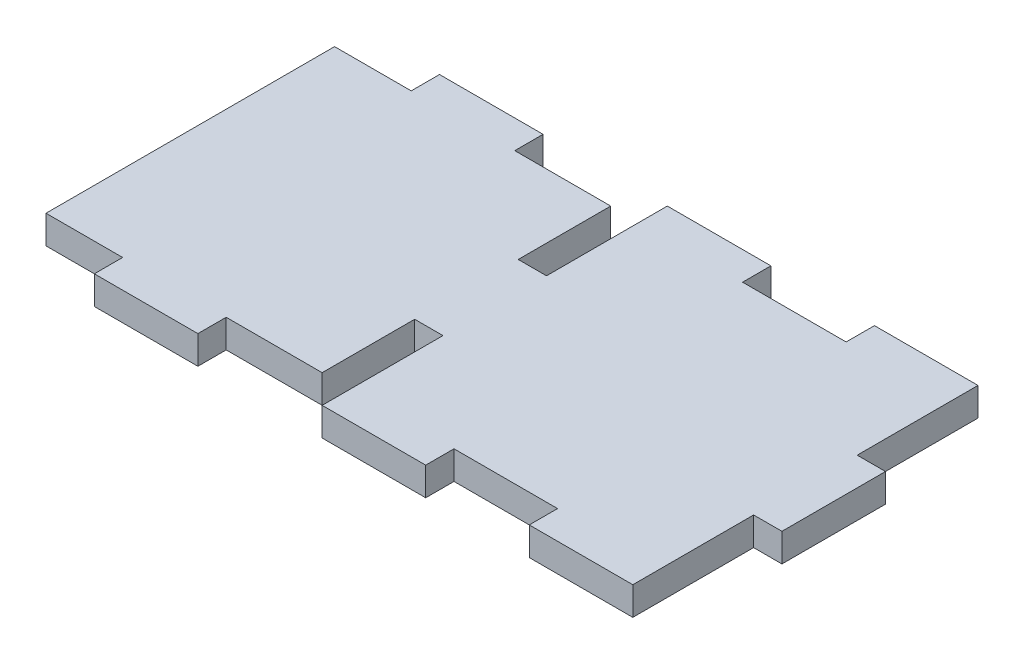
SolidWorks part; units mm, degrees
material "Corrugated Paper"
ref_plane "Front Plane" through (0, 0, 0) normal (0, 0, 1) x (1, 0, 0)
ref_plane "Top Plane" through (0, 0, 0) normal (0, 1, 0) x (1, 0, 0)
ref_plane "Right Plane" through (0, 0, 0) normal (1, 0, 0) x (0, 0, -1)
sketch "Sketch1" plane through (0, 0, 0) normal (0, 1, 0) x (1, 0, 0)
  line L0 (0, 32.5) -> (-4.1, 32.5)
  line L1 (0, 0) -> (15, 0)
  line L2 (0, 50) -> (0, 0) construction
  line L3 (30, 0) -> (45, 0)
  line L4 (0, 0) -> (45, 0) construction
  line L5 (-4.1, 17.5) -> (-4.1, 4.1)
  line L6 (-4.1, 17.5) -> (0, 17.5)
  line L7 (45, 32.5) -> (49.1, 32.5)
  line L8 (49.1, 32.5) -> (49.1, 17.5)
  line L9 (49.1, 17.5) -> (45, 17.5)
  line L10 (15, 50) -> (15, 45.9)
  line L11 (15, 45.9) -> (30, 45.9)
  line L12 (30, 45.9) -> (30, 50)
  line L13 (15, 0) -> (15, 4.1)
  line L14 (15, 4.1) -> (30, 4.1)
  line L15 (30, 4.1) -> (30, 0)
  line L16 (0, 50) -> (15, 50)
  line L17 (30, 50) -> (45, 50)
  line L18 (0, 50) -> (0, 32.5)
  line L19 (0, 17.5) -> (0, 0)
  line L20 (45, 0) -> (45, 17.5)
  line L21 (45, 32.5) -> (45, 50)
  line L22 (-33, 4.1) -> (-44.1, 4.1)
  line L24 (-4.1, 45.9) -> (-4.1, 32.5)
  line L25 (-4.1, 4.1) -> (-18, 4.1)
  line L26 (-44.1, 45.9) -> (-44.1, 4.1)
  line L27 (-44.1, 25) -> (49.1, 25) construction
  line L28 (-4.1, 45.9) -> (-18, 45.9)
  line L29 (-18, 4.1) -> (-18, 0)
  line L30 (-18, 0) -> (-33, 0)
  line L31 (-33, 4.1) -> (-33, 0)
  line L32 (-18, 45.9) -> (-18, 50)
  line L33 (-18, 50) -> (-33, 50)
  line L34 (-33, 45.9) -> (-33, 50)
  line L35 (-33, 45.9) -> (-44.1, 45.9)
  dimension "D1" = 50
  dimension "D2" = 45
  dimension "D3" = 4.1
  dimension "D4" = 15
  dimension "D5" = 15
  dimension "D6" = 33
  dimension "D7" = 40
extrude "Boss-Extrude1" add sketch "Sketch1" along normal blind 4.1
